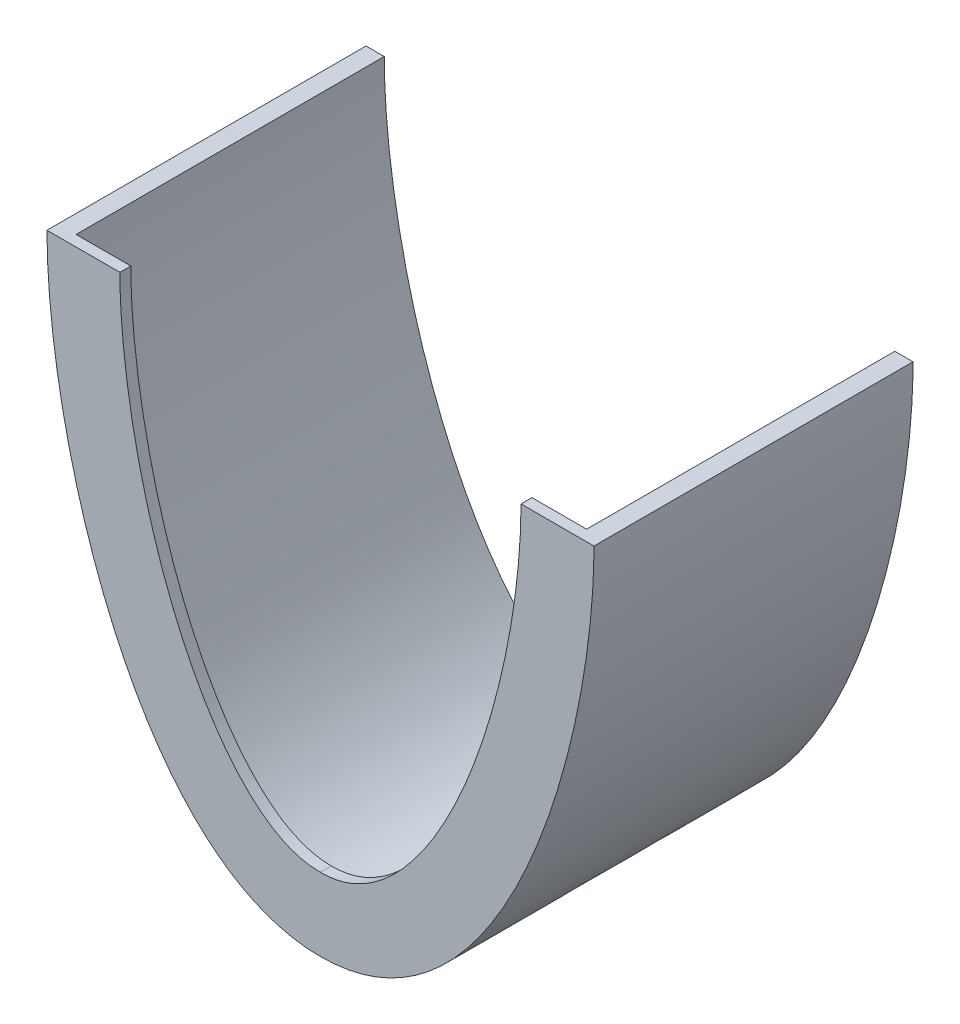
SolidWorks part; units mm, degrees
ref_plane "Ebene vorne" through (0, 0, 0) normal (0, 0, 1) x (1, 0, 0)
ref_plane "Ebene oben" through (0, 0, 0) normal (0, 1, 0) x (1, 0, 0)
ref_plane "Ebene rechts" through (0, 0, 0) normal (1, 0, 0) x (0, 0, -1)
sketch "Skizze1" plane through (0, 0, 0) normal (0, 0, 1) x (1, 0, 0)
  line L0 (0, 0) -> (-61888.4828, 0) construction
  line L1 (0, 0) -> (0, 61888.4828) construction
  line L2 (-75, 0) -> (-75, 61888.4828) construction
  line L3 (75, 0) -> (75, 61888.4828) construction
  line L4 (0, 135) -> (61888.4828, 135) construction
  line L5 (75, 76.0344) -> (75, 197.1624) construction
  line L6 (-75, 78.0769) -> (-75, 200.6937) construction
  line L7 (-45.3925, 0) -> (45.9427, 0) construction
  line L8 (39.5286, 0) -> (-61.7141, 0) construction
  line L9 (70, 135) -> (75, 135)
  line L10 (-70, 135) -> (-75, 135)
  spline S0 degree 3 poles (-75, 135) (-75, 85) (-50, 0) (0, 0) knots 0 0 0 0 1 1 1 1
  spline S1 degree 3 poles (75, 135) (75, 85) (50, 0) (0, 0) knots 0 0 0 0 1 1 1 1
  spline S2 degree 1 poles (-70, 135) (0, 5) knots 0 0 1 1 construction
  spline S3 degree 1 poles (70, 135) (0, 5) knots 0 0 1 1 construction
  spline S4 degree 3 poles (-70, 135) (-70, 134.2358) (-69.9882, 132.7202) (-69.9172, 129.5878) (-69.7393, 125.5625) (-69.3825, 120.5582) (-68.7152, 113.6942) (-67.5213, 104.8102) (-65.5132, 93.8512) (-62.9314, 82.7785) (-58.7288, 68.1083) (-52.0622, 50.4049) (-41.878, 31.6456) (-31.7156, 19.3087) (-22.739, 12.0686) (-16.8065, 8.7354) (-11.8611, 6.8278) (-8.0441, 5.7864) (-4.7591, 5.2536) (-2.0679, 5.0368) (-0.6866, 5) (0, 5) knots 0 0 0 0 0.015625 0.03125 0.0625 0.09375 0.125 0.1875 0.25 0.3125 0.375 0.5 0.625 0.75 0.8125 0.875 0.90625 0.9375 0.96875 0.984375 1 1 1 1
  spline S5 degree 3 poles (0, 5) (0.6866, 5) (2.0679, 5.0368) (4.7591, 5.2536) (8.0441, 5.7864) (11.8611, 6.8278) (16.8065, 8.7354) (22.739, 12.0686) (31.7156, 19.3087) (41.878, 31.6456) (52.0622, 50.4049) (58.7288, 68.1083) (62.9314, 82.7785) (65.5132, 93.8512) (67.5213, 104.8102) (68.7152, 113.6942) (69.3825, 120.5582) (69.7393, 125.5625) (69.9172, 129.5878) (69.9882, 132.7202) (70, 134.2358) (70, 135) knots 0 0 0 0 0.015625 0.03125 0.0625 0.09375 0.125 0.1875 0.25 0.375 0.5 0.625 0.6875 0.75 0.8125 0.875 0.90625 0.9375 0.96875 0.984375 1 1 1 1
  dimension "D4" = 150
  dimension "D5" = 150
  dimension "D6" = 150
  dimension "D7" = 150
  dimension "D1" = 150
  dimension "D2" = 75
  dimension "D3" = 135
  dimension "D8" = 5
extrude "Aufsatz-Linear austragen1" add sketch "Skizze1" against normal blind 87.5
sketch "Skizze2" plane through (0, 0, 0) normal (0, 0, 1) x (1, 0, 0)
  line L0 (70, 135) -> (55, 135)
  line L1 (-70, 135) -> (-55, 135)
  spline S0 degree 1 poles (55, 135) (0, 20) knots 0 0 1 1 construction
  spline S1 degree 3 poles (34.7838, 2134.5706) (57.9855, 177.2244) (70.8054, 168.7743) (69.9172, 129.5878) (69.7393, 125.5625) (69.3825, 120.5582) (68.7152, 113.6942) (67.5213, 104.8102) (65.5132, 93.8512) (62.9314, 82.7785) (58.7288, 68.1083) (52.0622, 50.4049) (41.878, 31.6456) (31.7156, 19.3087) (22.739, 12.0686) (16.8065, 8.7354) (11.8611, 6.8278) (8.0441, 5.7864) (4.7591, 5.2536) (-34.3147, 2.1058) (-100.1201, 55.365) (1985.0746, 243.9015) knots -0.719384 -0.719384 -0.719384 -0.719384 0.015625 0.03125 0.0625 0.09375 0.125 0.1875 0.25 0.3125 0.375 0.5 0.625 0.75 0.8125 0.875 0.90625 0.9375 0.96875 0.984375 1.84494 1.84494 1.84494 1.84494 only from (70, 135) to (0, 5) construction
  spline S2 degree 3 poles (-1985.0713, 243.9012) (100.12, 55.365) (34.3147, 2.1058) (-4.7591, 5.2536) (-8.0441, 5.7864) (-11.8611, 6.8278) (-16.8065, 8.7354) (-22.739, 12.0686) (-31.7156, 19.3087) (-41.878, 31.6456) (-52.0622, 50.4049) (-58.7288, 68.1083) (-62.9314, 82.7785) (-65.5132, 93.8512) (-67.5213, 104.8102) (-68.7152, 113.6942) (-69.3825, 120.5582) (-69.7393, 125.5625) (-69.9172, 129.5878) (-70.8054, 168.7743) (-57.9855, 177.2244) (-34.7837, 2134.5774) knots -0.844939 -0.844939 -0.844939 -0.844939 0.015625 0.03125 0.0625 0.09375 0.125 0.1875 0.25 0.375 0.5 0.625 0.6875 0.75 0.8125 0.875 0.90625 0.9375 0.96875 0.984375 1.719385 1.719385 1.719385 1.719385 only from (0, 5) to (-70, 135) construction
  spline S3 degree 3 poles (70, 135) (70, 134.2358) (69.9882, 132.7202) (69.9172, 129.5878) (69.7393, 125.5625) (69.3825, 120.5582) (68.7152, 113.6942) (67.5213, 104.8102) (65.5132, 93.8512) (62.9314, 82.7785) (58.7288, 68.1083) (52.0622, 50.4049) (41.878, 31.6456) (31.7156, 19.3087) (22.739, 12.0686) (16.8065, 8.7354) (11.8611, 6.8278) (8.0441, 5.7864) (4.7591, 5.2536) (2.0679, 5.0368) (0.6866, 5) (0, 5) knots 0 0 0 0 0.015625 0.03125 0.0625 0.09375 0.125 0.1875 0.25 0.3125 0.375 0.5 0.625 0.75 0.8125 0.875 0.90625 0.9375 0.96875 0.984375 1 1 1 1
  spline S4 degree 3 poles (0, 5) (-0.6866, 5) (-2.0679, 5.0368) (-4.7591, 5.2536) (-8.0441, 5.7864) (-11.8611, 6.8278) (-16.8065, 8.7354) (-22.739, 12.0686) (-31.7156, 19.3087) (-41.878, 31.6456) (-52.0622, 50.4049) (-58.7288, 68.1083) (-62.9314, 82.7785) (-65.5132, 93.8512) (-67.5213, 104.8102) (-68.7152, 113.6942) (-69.3825, 120.5582) (-69.7393, 125.5625) (-69.9172, 129.5878) (-69.9882, 132.7202) (-70, 134.2358) (-70, 135) knots 0 0 0 0 0.015625 0.03125 0.0625 0.09375 0.125 0.1875 0.25 0.375 0.5 0.625 0.6875 0.75 0.8125 0.875 0.90625 0.9375 0.96875 0.984375 1 1 1 1
  spline S5 degree 1 poles (0, 20) (-55, 135) knots 0 0 1 1 construction
  spline S6 degree 3 poles (55, 135) (55, 134.3126) (54.9894, 132.9533) (54.9251, 130.1103) (54.7629, 126.4357) (54.4343, 121.8229) (53.8159, 115.4602) (52.7025, 107.1703) (50.8224, 96.909) (48.4052, 86.5436) (44.4855, 72.8636) (38.3273, 56.5397) (30.7464, 42.6486) (24.179, 33.803) (19.1531, 28.4517) (14.1984, 24.4852) (10.244, 22.2857) (7.1602, 21.0998) (4.8583, 20.4728) (2.8865, 20.1534) (1.2727, 20.0229) (0.4206, 20) (0, 20) knots 0 0 0 0 0.015625 0.03125 0.0625 0.09375 0.125 0.1875 0.25 0.3125 0.375 0.5 0.625 0.6875 0.75 0.8125 0.875 0.90625 0.9375 0.96875 0.984375 1 1 1 1
  spline S7 degree 3 poles (0, 20) (-0.4206, 20) (-1.2727, 20.0229) (-2.8865, 20.1534) (-4.8583, 20.4728) (-7.1602, 21.0998) (-10.244, 22.2857) (-14.1984, 24.4852) (-19.1531, 28.4517) (-24.179, 33.803) (-30.7464, 42.6486) (-38.3273, 56.5397) (-44.4855, 72.8636) (-48.4052, 86.5436) (-50.8224, 96.909) (-52.7025, 107.1703) (-53.8159, 115.4602) (-54.4343, 121.8229) (-54.7629, 126.4357) (-54.9251, 130.1103) (-54.9894, 132.9533) (-55, 134.3126) (-55, 135) knots 0 0 0 0 0.015625 0.03125 0.0625 0.09375 0.125 0.1875 0.25 0.3125 0.375 0.5 0.625 0.6875 0.75 0.8125 0.875 0.90625 0.9375 0.96875 0.984375 1 1 1 1
  dimension "D1" = 15
extrude "Aufsatz-Linear austragen2" add sketch "Skizze2" against normal blind 3
sketch "Skizze10" plane through (0, 135, 0) normal (0, 1, 0) x (1, 0, 0)
  line L0 (0, 0) -> (0, -50000) construction
  line L1 (75, 0) -> (50075, 0) construction
  line L2 (0, 200) -> (50000, 200) construction
  line L3 (133.0405, 195) -> (50133.0405, 195) construction
  line L4 (75, 87.5) -> (70, 87.5)
  line L5 (-70, 87.5) -> (-75, 87.5)
  spline S0 degree 2 poles (75, 87.5) (0, 312.5) (-75, 87.5) knots 0 0 0 1 1 1
  spline S1 degree 2 poles (70, 87.5) (0, 302.5) (-70, 87.5) knots 0 0 0 1 1 1
  dimension "D1" = 200
  dimension "D2" = 5
sketch "Skizze11" plane through (0, 0, 0) normal (1, 0, 0) x (0, 0, -1)
  line L0 (200, 135) -> (87.5, 135) construction
  line L1 (200000, 135) -> (-250000, 135) construction
  line L2 (87.5, 0) -> (87.5, 135) construction
  line L4 (-93.7616, -84.5237) -> (268.7616, 84.5237) construction
  line L5 (195, 135) -> (87.5, 135) construction
  line L6 (148.2362, -58.1852) -> (251.7638, 328.1852) construction
  line L7 (-15.9917, 5) -> (-50015.9917, 5) construction
  line L8 (0, 0) -> (-50000, 0) construction
  spline S0 degree 3 poles (200, 135) (182.7454, 70.6049) (147.9205, 28.1746) (87.5, 0) knots 0 0 0 0 1 1 1 1
  dimension "D1" = 200
  dimension "D2" = 200
  dimension "D3" = 65
  dimension "D4" = 75
  dimension "D5" = 5
